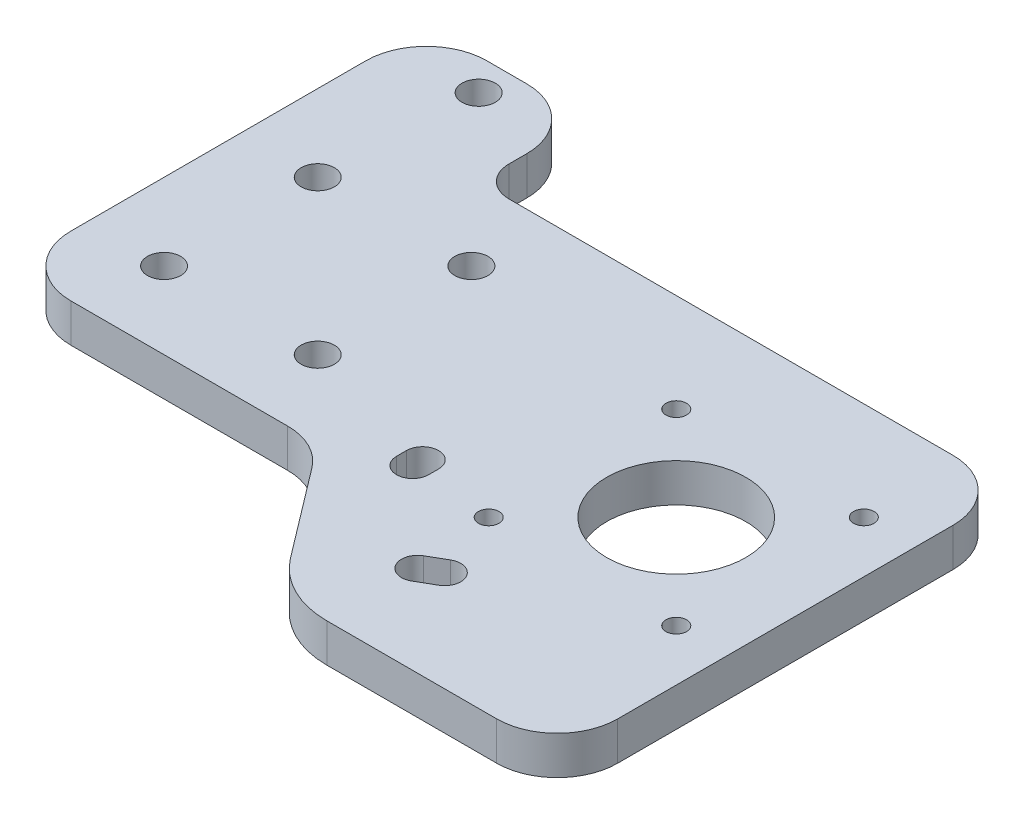
SolidWorks part; units mm, degrees
material "6061-T6 (SS)"
ref_plane "Front" through (0, 0, 0) normal (0, 0, 1) x (1, 0, 0)
ref_plane "Top" through (0, 0, 0) normal (0, 1, 0) x (1, 0, 0)
ref_plane "Right" through (0, 0, 0) normal (1, 0, 0) x (0, 0, -1)
sketch "Sketch1" plane through (0, 0, 0) normal (0, 1, 0) x (1, 0, 0)
  line L0 (0, 0) -> (89.6212, 0) construction
  line L1 (25.4, -25.4) -> (-25.4, -25.4)
  line L2 (25.4, -25.4) -> (25.4, 25.4) construction
  line L3 (25.4, 25.4) -> (-25.4, 25.4) construction
  line L4 (-25.4, -25.4) -> (-25.4, 25.4)
  line L5 (25.4, -25.4) -> (-25.4, 25.4) construction
  line L6 (25.4, 25.4) -> (-25.4, -25.4) construction
  line L7 (1.2, 25.4) -> (1.2, 76.2) construction
  line L8 (-12.7, 25.4) -> (-12.7, -25.4) construction
  line L9 (12.7, -25.4) -> (12.7, 25.4) construction
  line L10 (0, 0) -> (-25.4, 0) construction
  line L11 (-12.7, 0) -> (-12.7, 25.4) construction
  line L12 (-12.7, 12.7) -> (12.7, 12.7) construction
  line L13 (38.1, -41.4) -> (89.6212, -41.4) construction
  line L14 (86.6212, -27.36) -> (44.6212, -27.36) construction
  line L15 (86.6212, -27.36) -> (86.6212, 14.64) construction
  line L16 (86.6212, 14.64) -> (44.6212, 14.64) construction
  line L17 (44.6212, -27.36) -> (44.6212, 14.64) construction
  line L18 (86.6212, -27.36) -> (44.6212, 14.64) construction
  line L19 (86.6212, 14.64) -> (44.6212, -27.36) construction
  line L20 (81.1212, -21.86) -> (50.1212, -21.86) construction
  line L21 (81.1212, -21.86) -> (81.1212, 9.14) construction
  line L22 (81.1212, 9.14) -> (50.1212, 9.14) construction
  line L23 (50.1212, -21.86) -> (50.1212, 9.14) construction
  line L24 (81.1212, -21.86) -> (50.1212, 9.14) construction
  line L25 (81.1212, 9.14) -> (50.1212, -21.86) construction
  line L26 (89.6212, -41.4) -> (89.6212, 0) construction
  line L27 (36.4, -12.72) -> (65.6212, -12.72) construction
  line L28 (35.1664, -25.3192) -> (52.7755, -28.8008) construction
  line L29 (25.4, -25.4) -> (39.5919, -44.1062)
  line L30 (65.6212, 0) -> (0, 0) construction
  line L31 (1.2, 76.2) -> (-49.6, 76.2) construction
  line L32 (51.5419, -50.04) -> (89.6212, -50.04)
  line L33 (89.6212, -50.04) -> (89.6212, 25.4)
  line L34 (89.6212, 25.4) -> (25.4, 25.4)
  line L35 (36.4, -19.08) -> (36.4, -20.72) construction
  line L36 (51.5419, -35.04) -> (54.3783, -33.4) construction
  line L37 (51.5419, -35.04) -> (51.5419, -50.04) construction
  line L38 (-49.6, 76.2) -> (-49.6, 25.4) construction
  line L39 (-49.6, -25.4) -> (-25.4, -25.4) construction
  line L40 (-49.6, 25.4) -> (-25.4, 25.4) construction
  line L41 (-11.5, 25.4) -> (-11.5, 76.2) construction
  line L42 (-25.4, 25.4) -> (-25.4, 43.35)
  line L43 (-25.4, 43.35) -> (1.2, 43.35)
  line L44 (1.2, 43.35) -> (1.2, 25.4)
  line L45 (1.2, 25.4) -> (25.4, 25.4)
  circle A0 centre (-12.7, 12.7) radius 2.5 construction
  circle A1 centre (12.7, 12.7) radius 2.5 construction
  circle A2 centre (-12.7, -12.7) radius 2.5 construction
  circle A3 centre (12.7, -12.7) radius 2.5 construction
  circle A4 centre (65.6212, -6.36) radius 6.36 construction
  circle A5 centre (65.6212, -6.36) radius 11 construction
  circle A6 centre (50.1212, 9.14) radius 1.5 construction
  circle A7 centre (81.1212, 9.14) radius 1.5 construction
  circle A8 centre (81.1212, -21.86) radius 1.5 construction
  circle A9 centre (50.1212, -21.86) radius 1.5 construction
  circle A10 centre (51.5419, -35.04) radius 6.36 construction
  circle A11 centre (51.5419, -35.04) radius 11 construction
  circle A12 centre (36.4, -19.08) radius 6.36 construction
  circle A13 centre (36.4, -19.08) radius 11 construction
  circle A14 centre (50.1212, -21.86) radius 3 construction
  circle A15 centre (-11.5, 38.1) radius 2.5 construction
  circle A16 centre (-11.5, 38.1) radius 5.25 construction
  circle A19 centre (36.4, -19.08) radius 2.5 construction
  circle A20 centre (51.5419, -35.04) radius 2.5 construction
  circle A21 centre (65.6212, -6.36) radius 11 construction
  arc A22 (39.5919, -44.1062) -> (51.5419, -50.04) centre (51.5419, -35.04) ccw
  circle A23 centre (36.4, -20.72) radius 8 construction
  circle A24 centre (36.4, -20.72) radius 11 construction
  circle A25 centre (54.3783, -33.4) radius 8 construction
  circle A26 centre (54.3783, -33.4) radius 11 construction
  point P0 (0, 0)
  dimension "D6" = 5
  dimension "D7" = 12.72
  dimension "D9" = 22
  dimension "D11" = 3
  dimension "D12" = 16
  dimension "D13" = 6
  dimension "D16" = 12.7
  dimension "D17" = 5
  dimension "D18" = 22
  dimension "D20" = 16
  dimension "D21" = 4
  dimension "D23" = 10.5
  dimension "D1" = 50.8
  dimension "D2" = 50.8
  dimension "D3" = 50.8
  dimension "D4" = 12.7
  dimension "D5" = 25.4
  dimension "D8" = 42
  dimension "D10" = 31
  dimension "D14" = 50.8
  dimension "D15" = 24.2
  dimension "D19" = 3
  dimension "D22" = 12.7
extrude "Boss-Extrude1" add sketch "Sketch1" along normal blind 6.35
hole_wizard "M5 Clearance Hole1" positions "Sketch3" profile "Sketch2" hole size "M5" standard "ISO" end condition through all
sketch "Sketch3" plane through (0, 6.35, 0) normal (0, 1, 0) x (1, 0, 0)
  point P0 (-12.7, 12.7)
  point P3 (12.7, 12.7)
  point P6 (12.7, -12.7)
  point P9 (-12.7, -12.7)
  point P15 (-11.5, 38.1)
sketch "Sketch2" plane through (-12.7, 6.35, -12.7) normal (1, 0, 0) x (0, 0, 1)
  line L0 (0, 0) -> (0, 6.35)
  line L1 (0, 6.35) -> (2.75, 6.35)
  line L2 (2.75, 6.35) -> (2.75, 0)
  line L5 (2.75, 0) -> (0, 0)
  line L11 (0, -6.35) -> (0, 107.95) construction
  dimension "Thru Hole Dia." = 5.5
  dimension "Thru Hole Depth" = 6.35
sketch "Sketch7" plane through (0, 6.35, 0) normal (0, 1, 0) x (1, 0, 0)
  line L0 (36.4, -19.08) -> (36.4, -20.72) construction
  line L1 (54.3783, -33.4) -> (51.5419, -35.04) construction
  line L2 (53.0518, -31.1059) -> (50.2155, -32.7459)
  line L3 (33.75, -19.08) -> (33.75, -20.72)
  line L4 (55.7047, -35.6941) -> (52.8684, -37.3341)
  line L5 (39.05, -19.08) -> (39.05, -20.72)
  arc A0 (53.0518, -31.1059) -> (55.7047, -35.6941) centre (54.3783, -33.4) cw
  arc A1 (50.2155, -32.7459) -> (52.8684, -37.3341) centre (51.5419, -35.04) ccw
  arc A2 (33.75, -19.08) -> (39.05, -19.08) centre (36.4, -19.08) cw
  arc A3 (33.75, -20.72) -> (39.05, -20.72) centre (36.4, -20.72) ccw
  dimension "D1" = 2.65
  dimension "D2" = 2.65
extrude "Cut-Extrude2" cut sketch "Sketch7" against normal through all
fillet "Fillet1" radius 10 6 edges at (89.6212, 3.175, 50.04) (89.6212, 3.175, -25.4) (25.4, 3.175, 25.4) (-25.4, 3.175, 25.4) (-25.4, 3.175, -43.35) (1.2, 3.175, -43.35)
hole_wizard "M3 Clearance Hole1" positions "Sketch9" profile "Sketch8" hole size "M3" standard "ISO" end condition through all
sketch "Sketch9" plane through (0, 6.35, 0) normal (0, 1, 0) x (1, 0, 0)
  point P0 (50.1212, 9.14)
  point P3 (81.1212, 9.14)
  point P6 (81.1212, -21.86)
  point P9 (50.1212, -21.86)
sketch "Sketch8" plane through (50.1212, 6.35, -9.14) normal (1, 0, 0) x (0, 0, 1)
  line L0 (0, 0) -> (0, 6.35)
  line L1 (0, 6.35) -> (1.7, 6.35)
  line L2 (1.7, 6.35) -> (1.7, 0)
  line L5 (1.7, 0) -> (0, 0)
  line L11 (0, -6.35) -> (0, 107.95) construction
  dimension "Thru Hole Dia." = 3.4
  dimension "Thru Hole Depth" = 6.35
sketch "Sketch10" plane through (0, 6.35, 0) normal (0, 1, 0) x (1, 0, 0)
  circle A0 centre (65.6212, -6.36) radius 11.5
  dimension "D1" = 23
extrude "Cut-Extrude3" cut sketch "Sketch10" against normal through all
fillet "Fillet2" radius 5 1 edges at (1.2, 3.175, -25.4)
